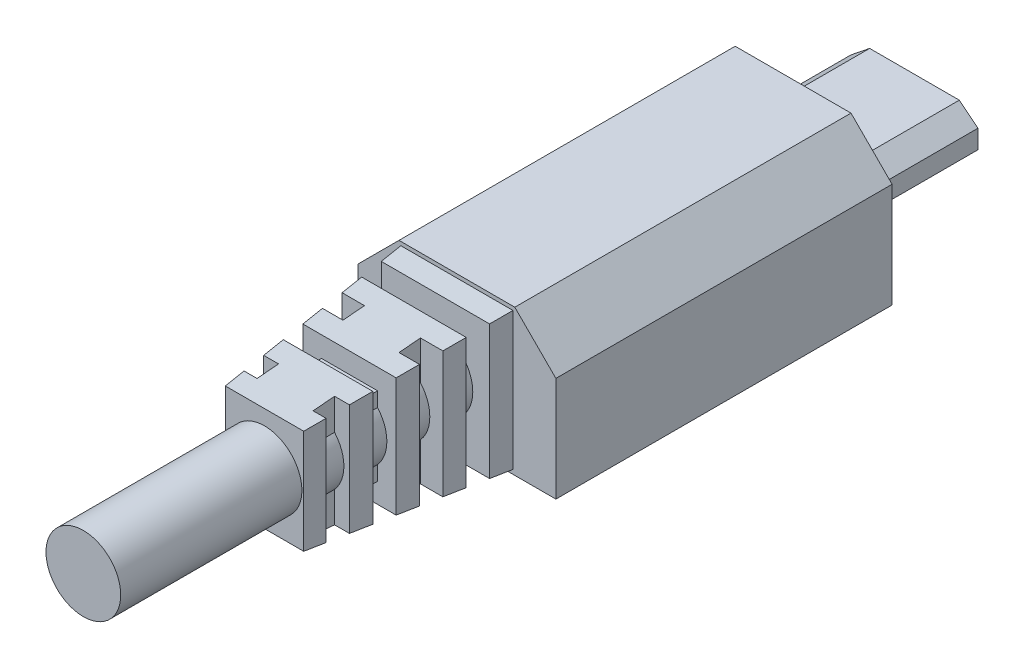
SolidWorks part; units mm, degrees
ref_plane "Front Plane" through (0, 0, 0) normal (0, 0, 1) x (1, 0, 0)
ref_plane "Top Plane" through (0, 0, 0) normal (0, 1, 0) x (1, 0, 0)
ref_plane "Right Plane" through (0, 0, 0) normal (1, 0, 0) x (0, 0, -1)
sketch "Sketch1" plane through (0, 0, 0) normal (0, 0, 1) x (1, 0, 0)
  line L0 (0, 1) -> (1, 1.8)
  line L1 (0, 0) -> (6.8, 0)
  line L2 (0, 0) -> (0, 1.8)
  line L3 (0, 1.8) -> (6.8, 1.8)
  line L4 (6.8, 0) -> (6.8, 1.8)
  line L5 (3.4, 1.8) -> (3.4, 0) construction
  line L6 (6.8, 1) -> (5.8, 1.8)
  line L8 (1.55, 0.2) -> (5.25, 0.2)
  line L9 (1.55, 0.2) -> (1.55, 0.85)
  line L10 (1.55, 0.85) -> (5.25, 0.85)
  line L11 (5.25, 0.2) -> (5.25, 0.85)
  point P15 (3.4, 0.85)
  dimension "D1" = 1.8
  dimension "D2" = 6.8
  dimension "D3" = 1
  dimension "D4" = 1
  dimension "D5" = 0.2
  dimension "D6" = 3.7
  dimension "D7" = 0.65
extrude "Boss-Extrude1" add sketch "Sketch1" along normal blind 6.5 contours L5 L3 L0 L2 L1 L8 L9 L10 | L3 L5 L10 L11 L8 L1 L4 L6
sketch "Sketch2" plane through (0, 0, 6.5) normal (0, 0, 1) x (1, 0, 0)
  line L0 (0, 0.7631) -> (-1.9, 0.7631) construction
  line L1 (-1.9, 4.8) -> (8.7, 4.8)
  line L2 (-1.9, 4.8) -> (-1.9, -3)
  line L3 (-1.9, -3) -> (8.7, -3)
  line L4 (8.7, 4.8) -> (8.7, -3)
  line L5 (-1.9, 2.6) -> (0.3, 4.8)
  line L6 (8.7, 2.6) -> (6.5, 4.8)
  line L7 (3.4, 4.8) -> (3.4, 1.8) construction
  line L8 (1, 1.8) -> (5.8, 1.8) construction
  line L9 (3.4, 0) -> (3.4, -3) construction
  line L10 (0, 0) -> (6.8, 0) construction
  line L13 (0, 0) -> (0, 1) construction
  line L14 (6.8, 0.7631) -> (8.7, 0.7631) construction
  line L15 (6.8, 0) -> (6.8, 1) construction
  line M1 (1.55, 0.85) -> (5.25, 0.85)
  line M2 (5.25, 0.85) -> (5.25, 0.2)
  line M3 (5.25, 0.2) -> (1.55, 0.2)
  line M4 (1.55, 0.2) -> (1.55, 0.85)
  line M5 (6.8, 1) -> (5.8, 1.8)
  line M6 (5.8, 1.8) -> (1, 1.8)
  line M7 (1, 1.8) -> (0, 1)
  line M8 (0, 1) -> (0, 0)
  line M9 (0, 0) -> (6.8, 0)
  line M10 (6.8, 0) -> (6.8, 1)
  dimension "D1" = 10.6
  dimension "D2" = 7.8
  dimension "D3" = 2.2
  dimension "D4" = 2.2
extrude "Boss-Extrude2" add sketch "Sketch2" along normal blind 18 contours L4 L6 L1 L5 L2 L3 M5 M10 M9 M8 M7 M6 | M10 M5 M6 M7 M8 M9 M4 M1 M2 M3 | M1 M4 M3 M2
sketch "Sketch5" plane through (0, 0, 24.5) normal (0, 0, 1) x (1, 0, 0)
  line L0 (0.3, 4.8) -> (6.5, 4.8) construction
  line L1 (6.4, 4.6) -> (0.4, 4.6)
  line L2 (6.4, 4.6) -> (6.4, -2.772)
  line L3 (6.4, -2.772) -> (0.4, -2.772)
  line L4 (0.4, 4.6) -> (0.4, -2.772)
  line L6 (3.4, 4.8) -> (3.4, 4.6) construction
  dimension "D1" = 0.2
  dimension "D2" = 6
extrude "Boss-Extrude4" add sketch "Sketch5" along normal blind 10.3 draft 5
sketch "Sketch7" plane through (0, 4.8, 0) normal (0, 1, 0) x (1, 0, 0)
  line L0 (3.4, -24.5) -> (3.4, -36.1996) construction
  line L1 (0.3, -24.5) -> (1.9, -24.5)
  line L2 (0.3, -24.5) -> (0.3, -25.65)
  line L3 (0.3, -25.65) -> (1.9, -25.65)
  line L4 (1.9, -24.5) -> (1.9, -25.65)
  line L5 (1.9, -25.65) -> (-0.2696, -25.65)
  line L6 (1.9, -25.65) -> (1.9, -26.8)
  line L7 (1.9, -26.8) -> (-0.2696, -26.8)
  line L8 (-0.2696, -25.65) -> (-0.2696, -26.8)
  line L9 (1.9, -26.8) -> (-0.2696, -26.8)
  line L10 (1.9, -26.8) -> (1.9, -27.95)
  line L11 (1.9, -27.95) -> (-0.2696, -27.95)
  line L12 (-0.2696, -26.8) -> (-0.2696, -27.95)
  line L13 (1.9, -27.95) -> (-0.2696, -27.95)
  line L14 (1.9, -27.95) -> (1.9, -29.1)
  line L15 (1.9, -29.1) -> (-0.2696, -29.1)
  line L16 (-0.2696, -27.95) -> (-0.2696, -29.1)
  line L17 (1.9, -29.1) -> (-0.2696, -29.1)
  line L18 (1.9, -29.1) -> (1.9, -30.25)
  line L19 (1.9, -30.25) -> (-0.2696, -30.25)
  line L20 (-0.2696, -29.1) -> (-0.2696, -30.25)
  line L21 (1.9, -30.25) -> (-0.2696, -30.25)
  line L22 (1.9, -30.25) -> (1.9, -31.4)
  line L23 (1.9, -31.4) -> (-0.2696, -31.4)
  line L24 (-0.2696, -30.25) -> (-0.2696, -31.4)
  line L25 (1.9, -31.4) -> (-0.2696, -31.4)
  line L26 (1.9, -31.4) -> (1.9, -32.55)
  line L27 (1.9, -32.55) -> (-0.2696, -32.55)
  line L28 (-0.2696, -31.4) -> (-0.2696, -32.55)
  line L29 (1.9, -32.55) -> (-0.2696, -32.55)
  line L30 (1.9, -32.55) -> (1.9, -33.7)
  line L31 (1.9, -33.7) -> (-0.2696, -33.7)
  line L32 (-0.2696, -32.55) -> (-0.2696, -33.7)
  line L33 (1.9, -33.7) -> (-0.2696, -33.7)
  line L34 (1.9, -33.7) -> (1.9, -34.85)
  line L35 (1.9, -34.85) -> (-0.2696, -34.85)
  line L36 (-0.2696, -33.7) -> (-0.2696, -34.85)
  line L37 (6.4, -24.5) -> (0.4, -24.5) construction
  line L38 (7.0696, -33.7) -> (7.0696, -34.85)
  line L39 (4.9, -34.85) -> (7.0696, -34.85)
  line L40 (4.9, -33.7) -> (4.9, -34.85)
  line L41 (4.9, -33.7) -> (7.0696, -33.7)
  line L42 (7.0696, -32.55) -> (7.0696, -33.7)
  line L43 (4.9, -33.7) -> (7.0696, -33.7)
  line L44 (4.9, -32.55) -> (4.9, -33.7)
  line L45 (4.9, -32.55) -> (7.0696, -32.55)
  line L46 (7.0696, -31.4) -> (7.0696, -32.55)
  line L47 (4.9, -32.55) -> (7.0696, -32.55)
  line L48 (4.9, -31.4) -> (4.9, -32.55)
  line L49 (4.9, -31.4) -> (7.0696, -31.4)
  line L50 (7.0696, -30.25) -> (7.0696, -31.4)
  line L51 (4.9, -31.4) -> (7.0696, -31.4)
  line L52 (4.9, -30.25) -> (4.9, -31.4)
  line L53 (4.9, -30.25) -> (7.0696, -30.25)
  line L54 (7.0696, -29.1) -> (7.0696, -30.25)
  line L55 (4.9, -30.25) -> (7.0696, -30.25)
  line L56 (4.9, -29.1) -> (4.9, -30.25)
  line L57 (4.9, -29.1) -> (7.0696, -29.1)
  line L58 (7.0696, -27.95) -> (7.0696, -29.1)
  line L59 (4.9, -29.1) -> (7.0696, -29.1)
  line L60 (4.9, -27.95) -> (4.9, -29.1)
  line L61 (4.9, -27.95) -> (7.0696, -27.95)
  line L62 (7.0696, -26.8) -> (7.0696, -27.95)
  line L63 (4.9, -27.95) -> (7.0696, -27.95)
  line L64 (4.9, -26.8) -> (4.9, -27.95)
  line L65 (4.9, -26.8) -> (7.0696, -26.8)
  line L66 (7.0696, -25.65) -> (7.0696, -26.8)
  line L67 (4.9, -26.8) -> (7.0696, -26.8)
  line L68 (4.9, -25.65) -> (4.9, -26.8)
  line L69 (4.9, -25.65) -> (7.0696, -25.65)
  line L70 (4.9, -24.5) -> (4.9, -25.65)
  line L71 (6.5, -25.65) -> (4.9, -25.65)
  line L72 (6.5, -24.5) -> (6.5, -25.65)
  line L73 (6.5, -24.5) -> (4.9, -24.5)
  dimension "D1" = 1.15
  dimension "D2" = 1.6
extrude "Cut-Extrude1" cut sketch "Sketch7" against normal blind 10.3 contours L5 L8 L7 L6 L3 | L11 L16 L15 L14 | L19 L24 L23 L22 | L27 L32 L31 L30 | L69 L68 L65 L66 | L61 L60 L57 L58 | L53 L52 L49 L50 | L45 L44 L41 L42
ref_plane "Plane1" through (6.4, -2.772, 24.5) normal (0, 1, 0) x (1, 0, 0)
sketch "Sketch9" plane through (8.7, 0, 0) normal (1, 0, 0) x (0, 0, -1)
  line L0 (-36.8785, 0.9) -> (-25.1788, 0.9) construction
  line L1 (-34.85, -2.8) -> (-34.85, -1.2)
  line L2 (-34.85, -2.8) -> (-33.7, -2.8)
  line L3 (-33.7, -2.8) -> (-33.7, -1.2)
  line L4 (-34.85, -1.2) -> (-33.7, -1.2)
  line L5 (-33.7, -1.2) -> (-33.7, -2.8)
  line L6 (-33.7, -1.2) -> (-32.55, -1.2)
  line L7 (-32.55, -1.2) -> (-32.55, -2.8)
  line L8 (-33.7, -2.8) -> (-32.55, -2.8)
  line L9 (-32.55, -1.2) -> (-32.55, -2.8)
  line L10 (-32.55, -1.2) -> (-31.4, -1.2)
  line L11 (-31.4, -1.2) -> (-31.4, -2.8)
  line L12 (-32.55, -2.8) -> (-31.4, -2.8)
  line L13 (-31.4, -1.2) -> (-31.4, -2.8)
  line L14 (-31.4, -1.2) -> (-30.25, -1.2)
  line L15 (-30.25, -1.2) -> (-30.25, -2.8)
  line L16 (-31.4, -2.8) -> (-30.25, -2.8)
  line L17 (-30.25, -1.2) -> (-30.25, -2.8)
  line L18 (-30.25, -1.2) -> (-29.1, -1.2)
  line L19 (-29.1, -1.2) -> (-29.1, -2.8)
  line L20 (-30.25, -2.8) -> (-29.1, -2.8)
  line L21 (-29.1, -1.2) -> (-29.1, -2.8)
  line L22 (-29.1, -1.2) -> (-27.95, -1.2)
  line L23 (-27.95, -1.2) -> (-27.95, -2.8)
  line L24 (-29.1, -2.8) -> (-27.95, -2.8)
  line L25 (-27.95, -1.2) -> (-27.95, -2.8)
  line L26 (-27.95, -1.2) -> (-26.8, -1.2)
  line L27 (-26.8, -1.2) -> (-26.8, -2.8)
  line L28 (-27.95, -2.8) -> (-26.8, -2.8)
  line L29 (-26.8, -1.2) -> (-26.8, -2.8)
  line L30 (-26.8, -1.2) -> (-25.65, -1.2)
  line L31 (-25.65, -1.2) -> (-25.65, -2.8)
  line L32 (-26.8, -2.8) -> (-25.65, -2.8)
  line L33 (-25.65, -1.2) -> (-25.65, -2.8)
  line L34 (-25.65, -1.2) -> (-24.5, -1.2)
  line L35 (-24.5, -1.2) -> (-24.5, -2.8)
  line L36 (-25.65, -2.8) -> (-24.5, -2.8)
  line L37 (-25.65, 4.6) -> (-24.5, 4.6)
  line L38 (-24.5, 3) -> (-24.5, 4.6)
  line L39 (-25.65, 3) -> (-24.5, 3)
  line L40 (-25.65, 3) -> (-25.65, 4.6)
  line L41 (-26.8, 4.6) -> (-25.65, 4.6)
  line L42 (-25.65, 3) -> (-25.65, 4.6)
  line L43 (-26.8, 3) -> (-25.65, 3)
  line L44 (-26.8, 3) -> (-26.8, 4.6)
  line L45 (-27.95, 4.6) -> (-26.8, 4.6)
  line L46 (-26.8, 3) -> (-26.8, 4.6)
  line L47 (-27.95, 3) -> (-26.8, 3)
  line L48 (-27.95, 3) -> (-27.95, 4.6)
  line L49 (-29.1, 4.6) -> (-27.95, 4.6)
  line L50 (-27.95, 3) -> (-27.95, 4.6)
  line L51 (-29.1, 3) -> (-27.95, 3)
  line L52 (-29.1, 3) -> (-29.1, 4.6)
  line L53 (-30.25, 4.6) -> (-29.1, 4.6)
  line L54 (-29.1, 3) -> (-29.1, 4.6)
  line L55 (-30.25, 3) -> (-29.1, 3)
  line L56 (-30.25, 3) -> (-30.25, 4.6)
  line L57 (-31.4, 4.6) -> (-30.25, 4.6)
  line L58 (-30.25, 3) -> (-30.25, 4.6)
  line L59 (-31.4, 3) -> (-30.25, 3)
  line L60 (-31.4, 3) -> (-31.4, 4.6)
  line L61 (-32.55, 4.6) -> (-31.4, 4.6)
  line L62 (-31.4, 3) -> (-31.4, 4.6)
  line L63 (-32.55, 3) -> (-31.4, 3)
  line L64 (-32.55, 3) -> (-32.55, 4.6)
  line L65 (-33.7, 4.6) -> (-32.55, 4.6)
  line L66 (-32.55, 3) -> (-32.55, 4.6)
  line L67 (-33.7, 3) -> (-32.55, 3)
  line L68 (-33.7, 3) -> (-33.7, 4.6)
  line L69 (-34.85, 3) -> (-33.7, 3)
  line L70 (-33.7, 4.6) -> (-33.7, 3)
  line L71 (-34.85, 4.6) -> (-33.7, 4.6)
  line L72 (-34.85, 4.6) -> (-34.85, 3)
  dimension "D1" = 1.15
  dimension "D2" = 1.6
  dimension "D3" = 2.1
extrude "Cut-Extrude2" cut sketch "Sketch9" against normal blind 10.3 contours L44 L43 L40 L41 | L60 L59 L56 L57 | L27 L32 L31 L30 | L11 L16 L15 L14
sketch "Sketch3" plane through (0, 0, 24.5) normal (0, 0, 1) x (1, 0, 0)
  line L0 (3.4, 4.8) -> (3.4, 0.9) construction
  line L1 (0.3, 4.8) -> (6.5, 4.8) construction
  line L2 (3.4, 0.9) -> (-1.9, 0.9) construction
  line L3 (-1.9, 2.6) -> (-1.9, -3) construction
  line L4 (3.4, 0.9) -> (3.4, -3) construction
  line L5 (-1.9, -3) -> (8.7, -3) construction
  line L6 (3.4, 0.9) -> (8.7, 0.9) construction
  line L7 (8.7, 2.6) -> (8.7, -3) construction
  line L8 (8.7, 4.8) -> (8.7, -3) construction
  circle A0 centre (3.4, 0.9) radius 2
extrude "Boss-Extrude3" add sketch "Sketch3" along normal blind 20
